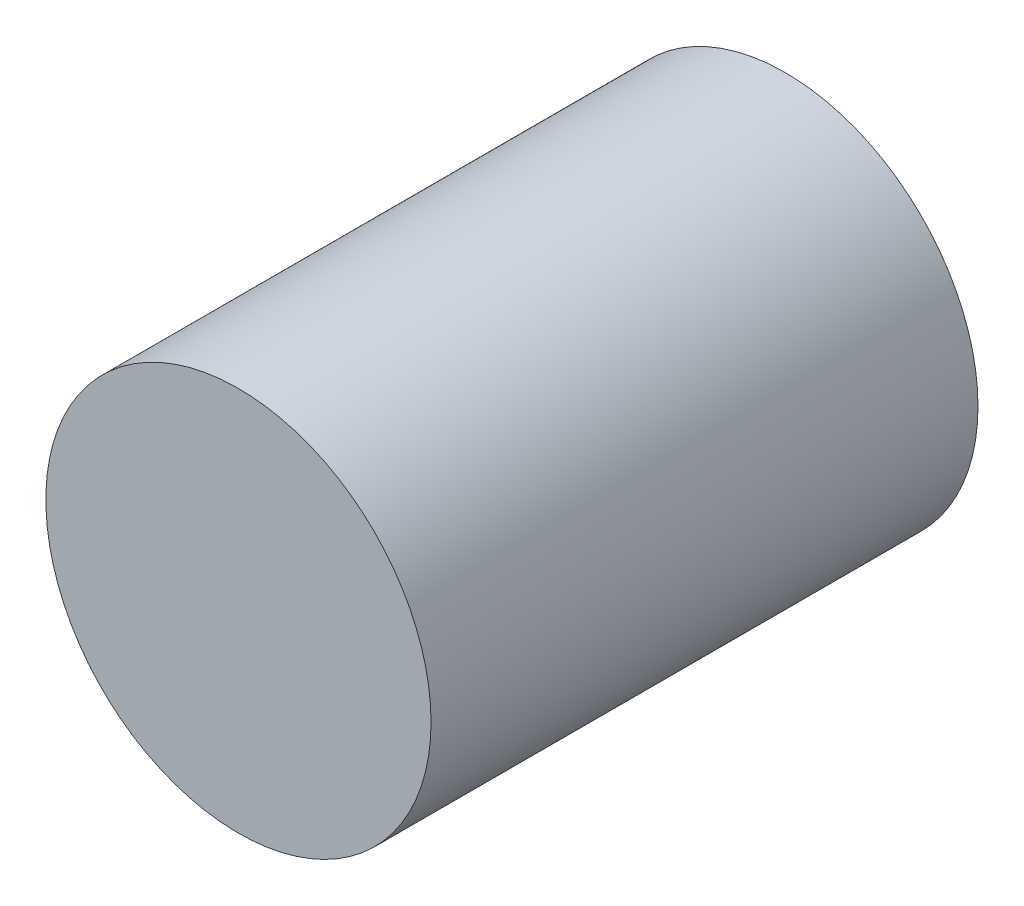
SolidWorks part; units mm, degrees
ref_plane "Front Plane" through (0, 0, 0) normal (0, 0, 1) x (1, 0, 0)
ref_plane "Top Plane" through (0, 0, 0) normal (0, 1, 0) x (1, 0, 0)
ref_plane "Right Plane" through (0, 0, 0) normal (1, 0, 0) x (0, 0, -1)
sketch "Sketch1" plane through (0, 0, 0) normal (0, 0, 1) x (1, 0, 0)
  circle A0 centre (0, 0) radius 5
  dimension "D1" = 10
extrude "Boss-Extrude1" add sketch "Sketch1" along normal blind 14.2
